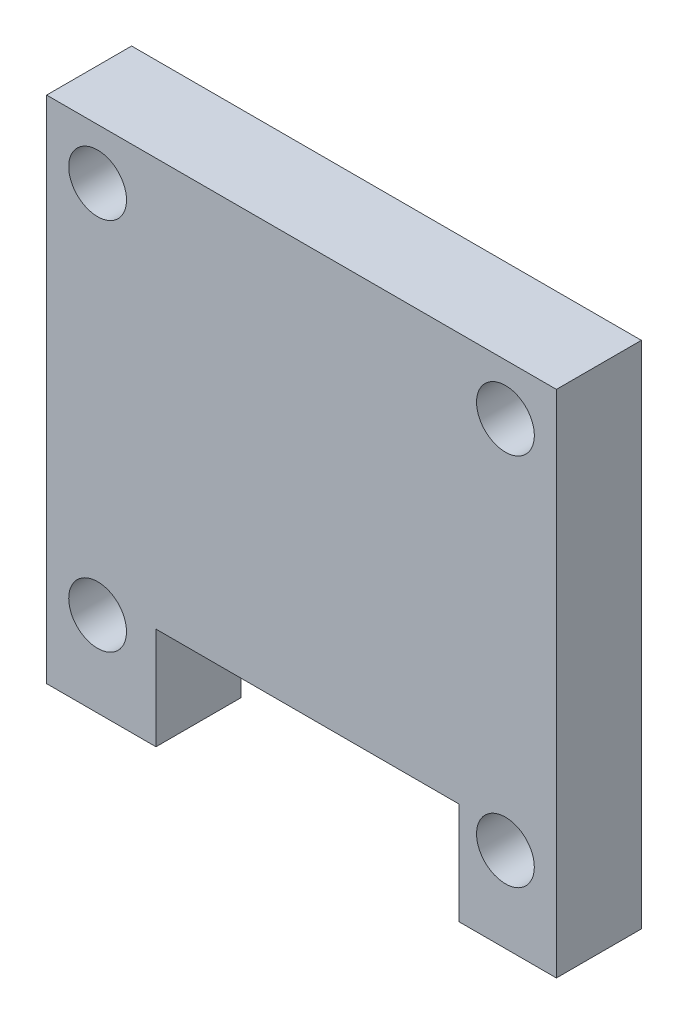
SolidWorks part; units mm, degrees
ref_plane "Front Plane" through (0, 0, 0) normal (0, 0, 1) x (1, 0, 0)
ref_plane "Top Plane" through (0, 0, 0) normal (0, 1, 0) x (1, 0, 0)
ref_plane "Right Plane" through (0, 0, 0) normal (1, 0, 0) x (0, 0, -1)
sketch "Sketch1" plane through (0, 0, 0) normal (0, 0, 1) x (1, 0, 0)
  line L0 (15, 30) -> (15, 0) construction
  line L1 (0, 0) -> (30, 0)
  line L2 (0, 0) -> (0, 30)
  line L3 (0, 30) -> (30, 30)
  line L4 (30, 0) -> (30, 30)
  circle A0 centre (3, 27) radius 1.7
  circle A1 centre (27, 27) radius 1.7
  circle A2 centre (27, 5) radius 1.7
  circle A3 centre (3, 5) radius 1.7
  point P9 (0, 0)
  point P17 (0, 0)
  dimension "D5" = 3.4
  dimension "D1" = 30
  dimension "D2" = 30
  dimension "D3" = 3
  dimension "D4" = 3
  dimension "D6" = 5
extrude "Boss-Extrude1" add sketch "Sketch1" along normal blind 5 contours L2 L3 L4 L1 | A0 | A3 | A2 | A1
sketch "Sketch3" plane through (0, 0, 5) normal (0, 0, 1) x (1, 0, 0)
  line L0 (0, 0) -> (30, 0) construction
  line L1 (6.4347, 0) -> (24.2653, 0)
  line L2 (6.4347, 0) -> (6.4347, 6)
  line L3 (6.4347, 6) -> (24.2653, 6)
  line L4 (24.2653, 0) -> (24.2653, 6)
  dimension "D1" = 6
extrude "Cut-Extrude1" cut sketch "Sketch3" against normal blind 5
